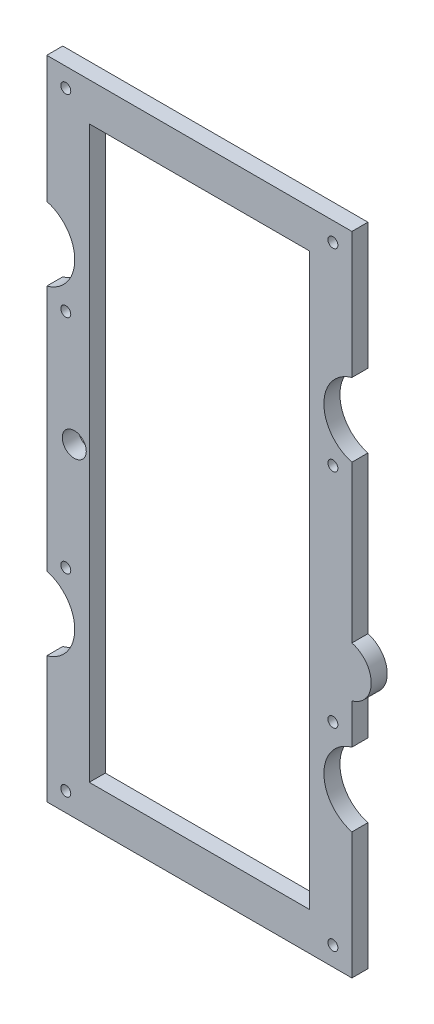
SolidWorks part; units mm, degrees
material "ABS"
ref_plane "Front Plane" through (0, 0, 0) normal (0, 0, 1) x (1, 0, 0)
ref_plane "Top Plane" through (0, 0, 0) normal (0, 1, 0) x (1, 0, 0)
ref_plane "Right Plane" through (0, 0, 0) normal (1, 0, 0) x (0, 0, -1)
sketch "Sketch1" plane through (0, 0, 0) normal (0, 0, 1) x (1, 0, 0)
  line L172 (-61.0801, -938.3303) -> (-61.0801, -1061.6697)
  line L173 (-61.0801, -1098.3303) -> (-61.0801, -1161.5626)
  line L174 (-61.0801, -1161.5626) -> (91.4199, -1161.5626)
  line L175 (91.4199, -1161.5626) -> (91.4199, -1098.3303)
  line L176 (91.4199, -1061.6697) -> (91.4199, -1041.5969)
  line L177 (91.4199, -1016.5631) -> (91.4199, -938.3303)
  line L178 (91.4199, -901.6697) -> (91.4199, -838.4374)
  line L179 (91.4199, -838.4374) -> (-61.0801, -838.4374)
  line L180 (-61.0801, -838.4374) -> (-61.0801, -901.6697)
  arc A81 (-61.0801, -938.3303) -> (-61.0801, -901.6697) centre (-66.0801, -920) ccw
  arc A82 (-61.0801, -1098.3303) -> (-61.0801, -1061.6697) centre (-66.0801, -1080) ccw
  arc A83 (91.4199, -1061.6697) -> (91.4199, -1098.3303) centre (96.4199, -1080) ccw
  arc A84 (91.4199, -1041.5969) -> (91.4199, -1016.5631) centre (88.1478, -1029.08) ccw
  arc A85 (91.4199, -901.6697) -> (91.4199, -938.3303) centre (96.4199, -920) ccw
  circle A131 centre (-51.5801, -847.9374) radius 2.5
  circle A137 centre (81.9199, -847.9374) radius 2.5
  circle A140 centre (81.9199, -944.5357) radius 2.5
  circle A143 centre (-51.5801, -944.5357) radius 2.5
  circle A146 centre (-51.5801, -1055.4643) radius 2.5
  circle A149 centre (81.9199, -1055.4643) radius 2.5
  circle A152 centre (81.9199, -1152.0626) radius 2.5
  circle A155 centre (-51.5801, -1152.0626) radius 2.5
extrude "Boss-Extrude1" add sketch "Sketch1" along normal blind 8 contours A81 L180 L179 L178 A85 L177 A84 L176 A83 L175 L174 L173 A82 L172
ref_plane "Plane1" through (0, 0, 4) normal (0, 0, 1) x (1, 0, 0)
sketch "Sketch3" plane through (0, 0, 8) normal (0, 0, 1) x (1, 0, 0)
  line L0 (91.4199, -977.4467) -> (-116.7456, -977.4467)
  line L1 (91.4199, -1016.5631) -> (91.4199, -938.3303) construction
  line L2 (-116.7456, -977.4467) -> (-212.7029, -785.3719)
  line L3 (-212.7029, -785.3719) -> (106.6532, -745.8336)
  line L4 (106.6532, -745.8336) -> (149.6809, -765.6027)
  line L5 (193.1812, -822.6125) -> (91.4199, -977.4467)
  line L6 (193.1812, -822.6125) -> (149.6809, -765.6027)
extrude "Cut-Extrude2" [suppressed] cut sketch "Sketch3" against normal through all
sketch "Sketch4" [suppressed] plane through (0, -977.4467, 0) normal (0, 1, 0) x (1, 0, 0)
  line L0 (-61.0801, -8) -> (-61.0801, 0) construction
  line L1 (-61.0801, -2) -> (-49.0801, -2)
  line L2 (-61.0801, -2) -> (-61.0801, -6)
  line L3 (-61.0801, -6) -> (-49.0801, -6)
  line L4 (-49.0801, -2) -> (-49.0801, -6)
  line L5 (91.4199, 0) -> (91.4199, -8) construction
  line L6 (91.4199, -2) -> (79.4199, -2)
  line L7 (91.4199, -2) -> (91.4199, -6)
  line L8 (91.4199, -6) -> (79.4199, -6)
  line L9 (79.4199, -2) -> (79.4199, -6)
  line L10 (67.4199, -8) -> (91.4199, -8) construction
  line L11 (-61.0801, 0) -> (-37.0801, 0) construction
  dimension "D1" = 12
  dimension "D2" = 4
  dimension "D3" = 2
  dimension "D4" = 4
  dimension "D5" = 2
  dimension "D6" = 12
extrude "Cut-Extrude3" [suppressed] cut sketch "Sketch4" against normal blind 10
sketch "Sketch5" plane through (0, 0, 0) normal (0, 0, -1) x (-1, 0, 0)
  line L0 (-91.4199, -1161.5626) -> (-91.4199, -1098.3303) construction
  line L1 (-70.1699, -857.5) -> (39.8301, -857.5)
  line L2 (-70.1699, -857.5) -> (-70.1699, -1142.5)
  line L3 (-70.1699, -1142.5) -> (39.8301, -1142.5)
  line L4 (39.8301, -857.5) -> (39.8301, -1142.5)
  line L5 (61.0801, -1161.5626) -> (-91.4199, -1161.5626) construction
  dimension "D1" = 285
  dimension "D2" = 110
  dimension "D3" = 21.25
  dimension "D4" = 19.0626
extrude "Cut-Extrude4" cut sketch "Sketch5" against normal through all
sketch "Sketch6" plane through (0, 0, 8) normal (0, 0, 1) x (1, 0, 0)
  line L0 (-39.8301, -1142.5) -> (-39.8301, -857.5) construction
  circle A0 centre (-47.3301, -1000) radius 6
  dimension "D1" = 12
  dimension "D2" = 7.5
extrude "Cut-Extrude5" cut sketch "Sketch6" against normal through all
